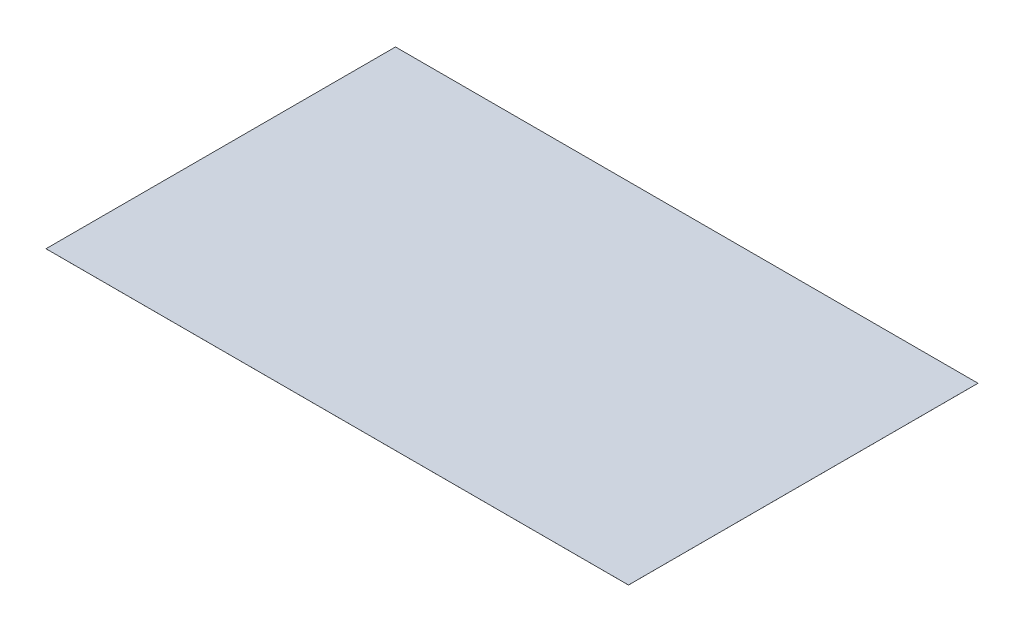
SolidWorks part; units mm, degrees
ref_plane "Plan de face" through (0, 0, 0) normal (0, 0, 1) x (1, 0, 0)
ref_plane "Plan de dessus" through (0, 0, 0) normal (0, 1, 0) x (1, 0, 0)
ref_plane "Plan de droite" through (0, 0, 0) normal (1, 0, 0) x (0, 0, -1)
sketch "Esquisse1" plane through (0, 0, 0) normal (0, 1, 0) x (1, 0, 0)
  line L1 (-12500, 7500) -> (12500, 7500)
  line L2 (-12500, 7500) -> (-12500, -7500)
  line L3 (-12500, -7500) -> (12500, -7500)
  line L4 (12500, 7500) -> (12500, -7500)
  line L5 (-12500, 7500) -> (12500, -7500) construction
  line L6 (-12500, -7500) -> (12500, 7500) construction
  point P0 (0, 0)
  dimension "D1" = 25000
  dimension "D2" = 15000
extrude "Boss.-Extru.1" add sketch "Esquisse1" along normal blind 1
